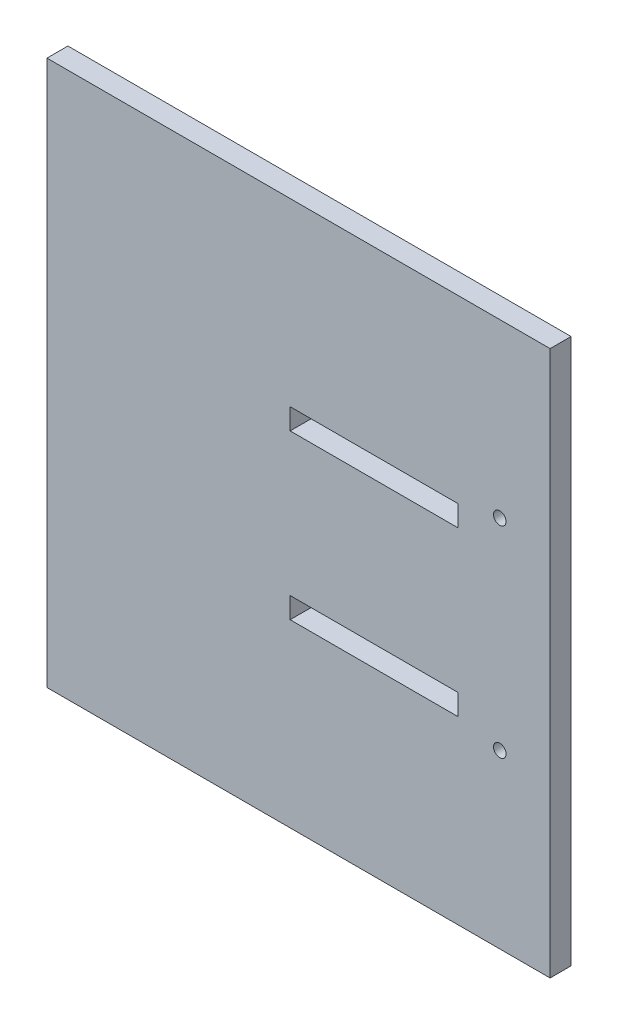
SolidWorks part; units mm, degrees
ref_plane "Front" through (0, 0, 0) normal (0, 0, 1) x (1, 0, 0)
ref_plane "Top" through (0, 0, 0) normal (0, 1, 0) x (1, 0, 0)
ref_plane "Right" through (0, 0, 0) normal (1, 0, 0) x (0, 0, -1)
sketch "Sketch2" plane through (0, 0, 0) normal (0, 0, 1) x (1, 0, 0)
  line L1 (-60, 65) -> (60, 65)
  line L2 (-60, 65) -> (-60, -65)
  line L3 (-60, -65) -> (60, -65)
  line L4 (60, 65) -> (60, -65)
  line L5 (-60, 65) -> (60, -65) construction
  line L6 (-60, -65) -> (60, 65) construction
  point P0 (0, 0)
  dimension "D1" = 130
  dimension "D2" = 120
extrude "Boss-Extrude1" add sketch "Sketch2" along normal blind 5
sketch "Sketch3" plane through (0, 0, 0) normal (0, 0, 1) x (1, 0, 0)
  line L0 (60, 0) -> (-60, 0) construction
  line L1 (38, 22) -> (-2, 22)
  line L2 (38, 22) -> (38, 17)
  line L3 (38, 17) -> (-2, 17)
  line L4 (-2, 22) -> (-2, 17)
  line L5 (38, 22) -> (-2, 17) construction
  line L6 (38, 17) -> (-2, 22) construction
  line L7 (60, -65) -> (60, 65) construction
  line L8 (50, 0) -> (-50, 0) construction
  line L9 (38, -17) -> (-2, -17)
  line L10 (-2, -22) -> (-2, -17)
  line L11 (38, -22) -> (-2, -22)
  line L12 (38, -22) -> (38, -17)
  line L13 (60, -65) -> (60, 65) construction
  line L14 (-60, 65) -> (-60, -65) construction
  circle A0 centre (48, 24) radius 1.5
  circle A1 centre (48, -24) radius 1.5
  point P0 (18, 19.5)
  dimension "D5" = 3
  dimension "D1" = 40
  dimension "D2" = 5
  dimension "D3" = 22
  dimension "D4" = 34
  dimension "D6" = 12
  dimension "D7" = 48
extrude "Cut-Extrude1" cut sketch "Sketch3" along normal through all
ref_plane "Plane1" through (60, 0, 0) normal (1, 0, 0) x (0, 0, -1)
sketch "Sketch4" plane through (60, 0, 0) normal (1, 0, 0) x (0, 0, -1)
  line L0 (0, 0) -> (-5, 0) construction
  line L1 (-5, -65) -> (-5, 65) construction
